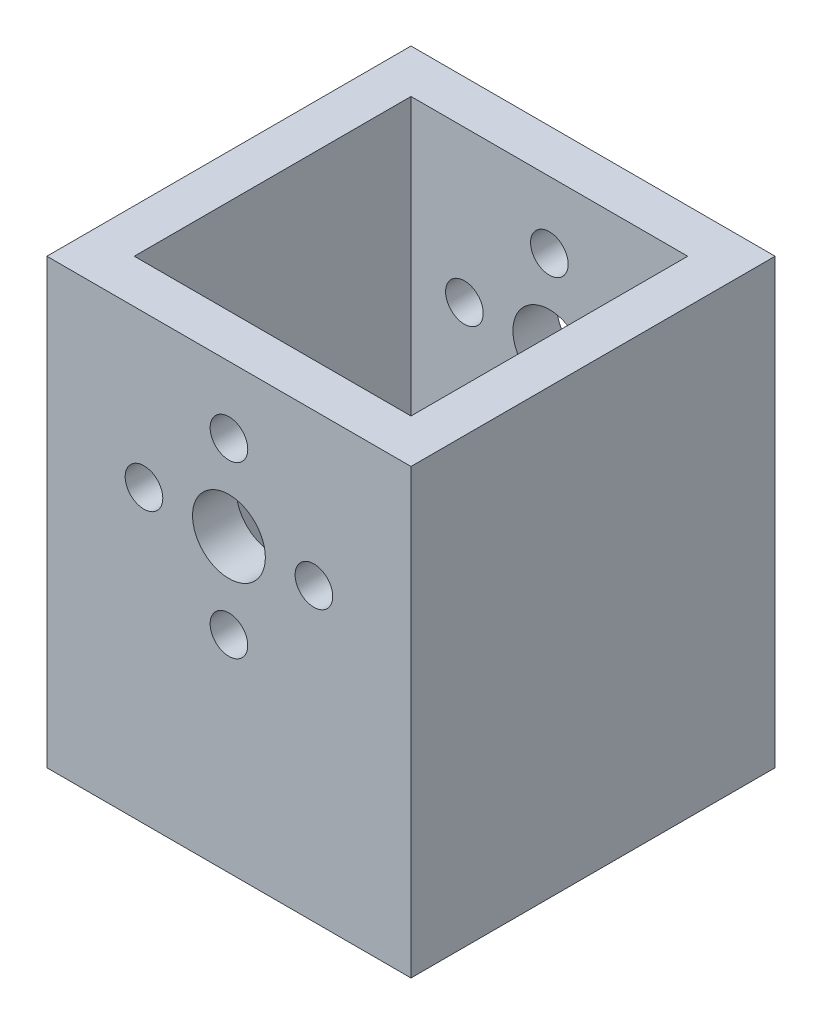
SolidWorks part; units mm, degrees
ref_plane "前视基准面" through (0, 0, 0) normal (0, 0, 1) x (1, 0, 0)
ref_plane "上视基准面" through (0, 0, 0) normal (0, 1, 0) x (1, 0, 0)
ref_plane "右视基准面" through (0, 0, 0) normal (1, 0, 0) x (0, 0, -1)
sketch "草图1" plane through (0, 0, 0) normal (0, 0, 1) x (1, 0, 0)
  line L0 (0, 0) -> (7, 0)
  line L1 (15, 0) -> (15, 12.5)
  line L2 (0, 12.5) -> (15, 12.5)
  line L3 (-15, 12.5) -> (-15, -24)
  line L4 (15, 0) -> (15, -24)
  line L5 (15, -24) -> (-15, -24)
  line L6 (0, 0) -> (0, 7)
  line L7 (0, 0) -> (0, -7)
  line L8 (0, 0) -> (-7, 0)
  line L9 (0, 0) -> (0, -19) construction
  line L25 (0, 12.5) -> (-15, 12.5)
  circle A0 centre (0, 0) radius 3
  circle A1 centre (0, 7) radius 1.55
  circle A2 centre (7, 0) radius 1.55
  circle A3 centre (0, -7) radius 1.55
  circle A4 centre (-7, 0) radius 1.55
extrude "凸台-拉伸1" add sketch "草图1" along normal blind 30
sketch "草图2" plane through (0, 12.5, 0) normal (0, 1, 0) x (1, 0, 0)
  line L0 (0, 0) -> (0, -30) construction
  line L1 (-15, 0) -> (15, 0) construction
  line L2 (-15, -30) -> (15, -30) construction
  line L3 (0, -30) -> (11.4, -30) construction
  line L4 (0, -30) -> (-11.1, -30) construction
  line L5 (-11.4, -15) -> (-11.4, -3.6)
  line L6 (-11.1, 0) -> (11.1, 0) construction
  line L7 (-11.4, -15) -> (-11.4, -26.4)
  line L8 (0, -26.4) -> (-11.4, -26.4)
  line L9 (11.4, -3.6) -> (11.4, -26.4)
  line L10 (0, -3.6) -> (11.4, -3.6)
  line L11 (11.4, -26.4) -> (0, -26.4)
  line L12 (0, -3.6) -> (-11.4, -3.6)
  point P16 (0, 0)
  point P17 (0, 0)
  point P19 (0, 0)
extrude "切除-拉伸1" cut sketch "草图2" against normal blind 33.5
